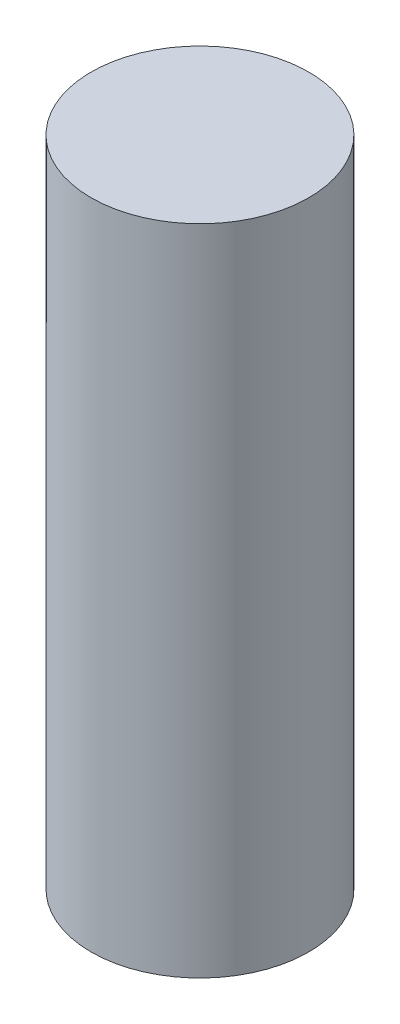
SolidWorks part; units mm, degrees
material "Cast Alloy Steel"
ref_plane "Front Plane" through (0, 0, 0) normal (0, 0, 1) x (1, 0, 0)
ref_plane "Top Plane" through (0, 0, 0) normal (0, 1, 0) x (1, 0, 0)
ref_plane "Right Plane" through (0, 0, 0) normal (1, 0, 0) x (0, 0, -1)
sketch "Sketch1" plane through (0, 0, 0) normal (0, 1, 0) x (1, 0, 0)
  circle A0 centre (0, 0) radius 10
  dimension "D1" = 20
extrude "Boss-Extrude1" add sketch "Sketch1" along normal blind 60 contours A0
